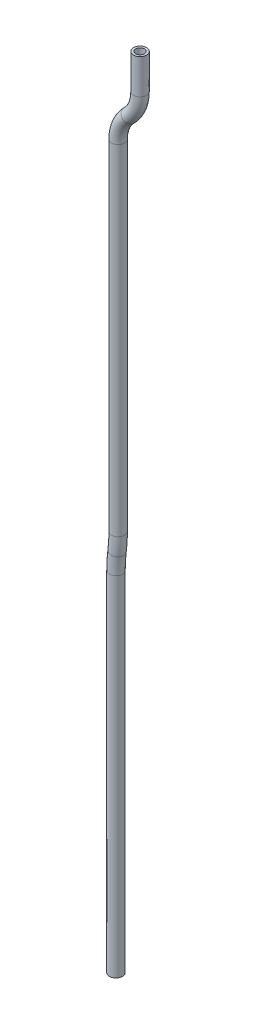
SolidWorks part; units mm, degrees
material "Alloy Steel (SS)"
ref_plane "Front Plane" through (0, 0, 0) normal (0, 0, 1) x (1, 0, 0)
ref_plane "Top Plane" through (0, 0, 0) normal (0, 1, 0) x (1, 0, 0)
ref_plane "Right Plane" through (0, 0, 0) normal (1, 0, 0) x (0, 0, -1)
sketch "Sketch1" plane through (0, 0, 0) normal (0, 0, 1) x (1, 0, 0)
  line L0 (0, 0) -> (0, 254)
  line L1 (17.553, 590.55) -> (17.553, 565.15)
  line L2 (1.5875, 527.05) -> (1.5875, 279.4)
  arc A0 (1.5875, 527.05) -> (9.5702, 546.1) centre (28.3093, 527.05) cw
  arc A1 (9.5702, 546.1) -> (17.553, 565.15) centre (-9.1688, 565.15) ccw
  arc A2 (0, 254) -> (0.7937, 266.7) centre (101.9969, 254) cw
  arc A3 (0.7937, 266.7) -> (1.5875, 279.4) centre (-100.4094, 279.4) ccw
  dimension "D3" = 25.4
  dimension "D4" = 38.1
  dimension "D1" = 17.553
  dimension "D5" = 25.4
  dimension "D6" = 590.55
  dimension "D7" = 254
  dimension "D2" = 1.5875
sketch "Sketch2" plane through (0, 0, 0) normal (0, 1, 0) x (1, 0, 0)
  circle A0 centre (0, 0) radius 4.7625
  circle A1 centre (0, 0) radius 3.175
  dimension "D1" = 9.525
  dimension "D2" = 1.5875
sweep "Sweep1" add profiles "Sketch2" path "Sketch1"
equation "\"D1@Sketch1\"=1.75529827cm"
